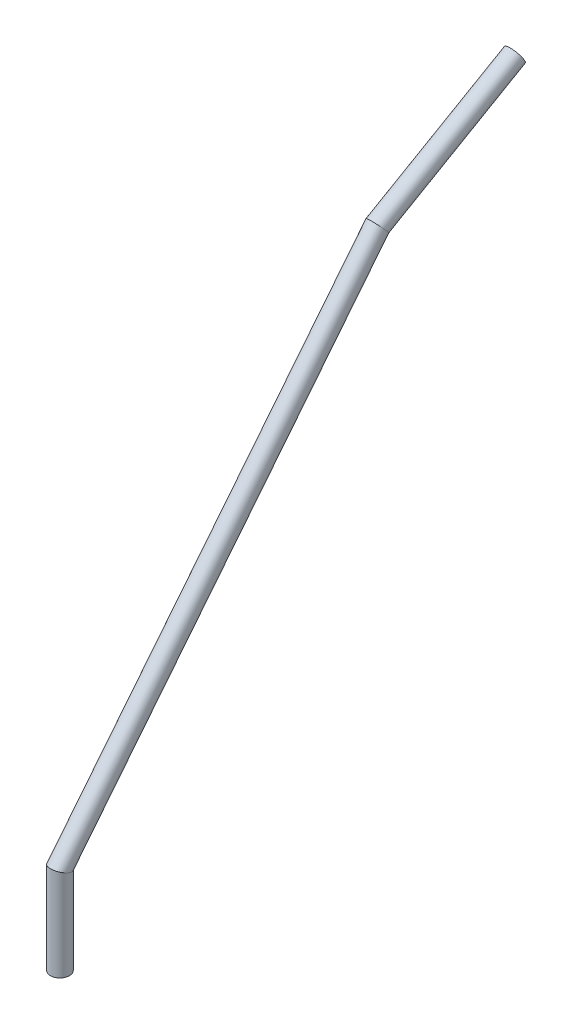
SolidWorks part; units mm, degrees
material "Silicon Rubber"
ref_plane "Front Plane" through (0, 0, 0) normal (0, 0, 1) x (1, 0, 0)
ref_plane "Top Plane" through (0, 0, 0) normal (0, 1, 0) x (1, 0, 0)
ref_plane "Right Plane" through (0, 0, 0) normal (1, 0, 0) x (0, 0, -1)
sketch "Sketch2" plane through (0, 0, 0) normal (0, 1, 0) x (1, 0, 0)
  line L0 (0, 2.5) -> (0, 8) construction
  line L1 (-17.5, 0) -> (17.5, 0) construction
  circle A0 centre (0, 0) radius 17.5 construction
  circle A1 centre (0, 0) radius 2.5 construction
  circle A2 centre (0, 8) radius 3.175
  circle A3 centre (0, 8) radius 4.7625
  circle A4 centre (0, -8) radius 3.175 construction
  circle A5 centre (0, -8) radius 4.7625 construction
  dimension "D1" = 35
  dimension "D2" = 5
  dimension "D4" = 6.35
  dimension "D5" = 9.525
  dimension "D3" = 5.5
sketch "Sketch4" plane through (0, 0, 0) normal (1, 0, 0) x (0, 0, -1)
  line L0 (8, 0) -> (8, 45)
  line L1 (8, 45) -> (168, 45) construction
  line L2 (168, 45) -> (168, 245) construction
  line L3 (8, 45) -> (168, 245)
  line L4 (168, 245) -> (237.282, 285)
  line L5 (168, 245) -> (193.0677, 245) construction
  dimension "D1" = 45
  dimension "D2" = 160
  dimension "D3" = 200
  dimension "D4" = 80
  dimension "D5" = 30
sweep "Sweep2" add profiles "Sketch2" path "Sketch4"
ref_plane "Plane2" through (0, 158.9961, -275.3894) normal (0, 0.5, -0.866) x (1, 0, 0)
sketch "Sketch11" plane through (0, 158.9961, -275.3894) normal (0, 0.5, -0.866) x (1, 0, 0)
  line L0 (0, -123.4137) -> (0, -132.9387) construction
  line L1 (-4.7625, -128.1762) -> (4.7625, -128.1762) construction
  line L2 (0, -123.4137) -> (2, -123.4137) construction
  line L3 (0, -123.4137) -> (-2, -123.4137) construction
  line L4 (-2, -123.4137) -> (-2, -128.1762)
  line L5 (-2, -128.1762) -> (2, -128.1762)
  line L6 (2, -128.1762) -> (2, -123.4137)
  line L7 (2, -123.4137) -> (-2, -123.4137)
  circle A0 centre (0, -128.1762) radius 4.7625 construction
  dimension "D1" = 2
extrude "Cut-Extrude2" cut sketch "Sketch11" against normal blind 8
